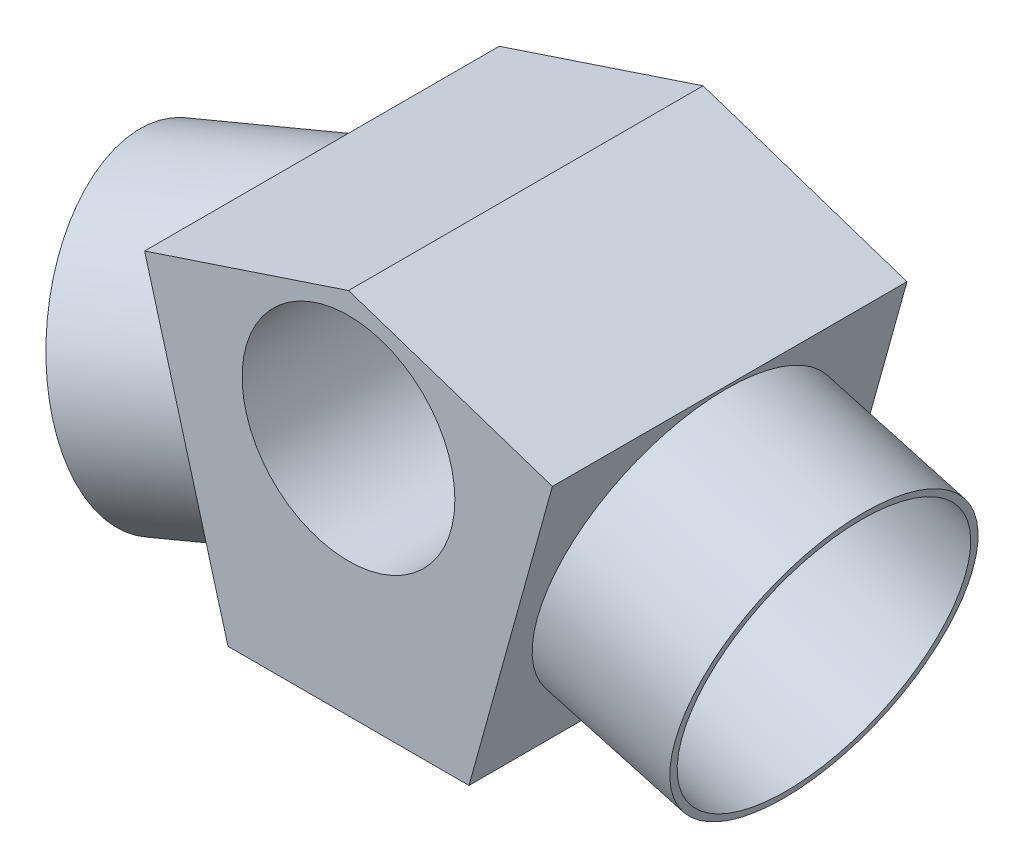
SolidWorks part; units mm, degrees
material "ABS"
ref_plane "Front Plane" through (0, 0, 0) normal (0, 0, 1) x (1, 0, 0)
ref_plane "Top Plane" through (0, 0, 0) normal (0, 1, 0) x (1, 0, 0)
ref_plane "Right Plane" through (0, 0, 0) normal (1, 0, 0) x (0, 0, -1)
sketch "Sketch2" plane through (0, 0, 0) normal (0, 0, 1) x (1, 0, 0)
  line L0 (0, 9.0224) -> (-14.3743, 4.2487)
  line L1 (-14.3743, 4.2487) -> (-8.495, -16.9512)
  line L2 (-8.495, -16.9512) -> (8.495, -16.9512)
  line L3 (0, -55) -> (0, 55) construction
  line L4 (14.3743, 4.2487) -> (8.495, -16.9512)
  line L5 (0, 9.0224) -> (14.3743, 4.2487)
  circle A0 centre (0, 0) radius 7.5
  point P10 (0, -16.9512)
  dimension "D1" = 15
  dimension "D2" = 105.5
extrude "Boss-Extrude1" add sketch "Sketch2" against normal blind 25
sketch "Sketch13" plane through (-12.2536, -3.3982, 0) normal (-0.9636, -0.2672, 0) x (0, 0, 1)
  line L0 (-12.5, 7.9355) -> (-12.5, -14.0645) construction
  line L1 (-25, 7.9355) -> (0, 7.9355) construction
  line L2 (-25, -14.0645) -> (0, -14.0645) construction
ref_plane "Plane6" through (-8.9816, -2.4908, 2.1589) normal (0.9388, 0.2603, -0.2257) x (0.2672, -0.9636, 0)
sketch "Sketch14" plane through (-8.9816, -2.4908, 2.1589) normal (0.9388, 0.2603, -0.2257) x (0.2672, -0.9636, 0)
  line L0 (-7.9355, 15.0471) -> (14.0645, 15.0471) construction
  circle A0 centre (3.0645, 15.0471) radius 10
  point P4 (3.0645, 15.0471)
  dimension "D1" = 20
extrude "Extrude-Thin3" add sketch "Sketch14" against normal blind 12 and the other way blind 3 thin
ref_plane "Plane4" through (20, 0, 0) normal (1, 0, 0) x (0, 0, -1)
sketch "Sketch7" plane through (20, 0, 0) normal (1, 0, 0) x (0, 0, -1)
  line L0 (0, -13.1465) -> (25, -13.1465) construction
  line L1 (0, -16.9512) -> (0, 4.2487) construction
  line L2 (25, -16.9512) -> (25, 4.2487) construction
ref_plane "Plane5" through (21.9571, -6.0893, 0) normal (0.9636, -0.2672, 0) x (0, 0, -1)
sketch "Sketch8" plane through (21.9571, -6.0893, 0) normal (0.9636, -0.2672, 0) x (0, 0, -1)
  circle A0 centre (12.3158, -2.8196) radius 10
  dimension "D1" = 20
extrude "Cut-Extrude4" cut sketch "Sketch8" against normal blind 13 contours A0
sketch "Sketch12" plane through (21.9571, -6.0893, 0) normal (0.9636, -0.2672, 0) x (0, 0, -1)
  circle A0 centre (12.3158, -2.8196) radius 10
extrude "Extrude-Thin2" add sketch "Sketch12" against normal blind 12 thin
